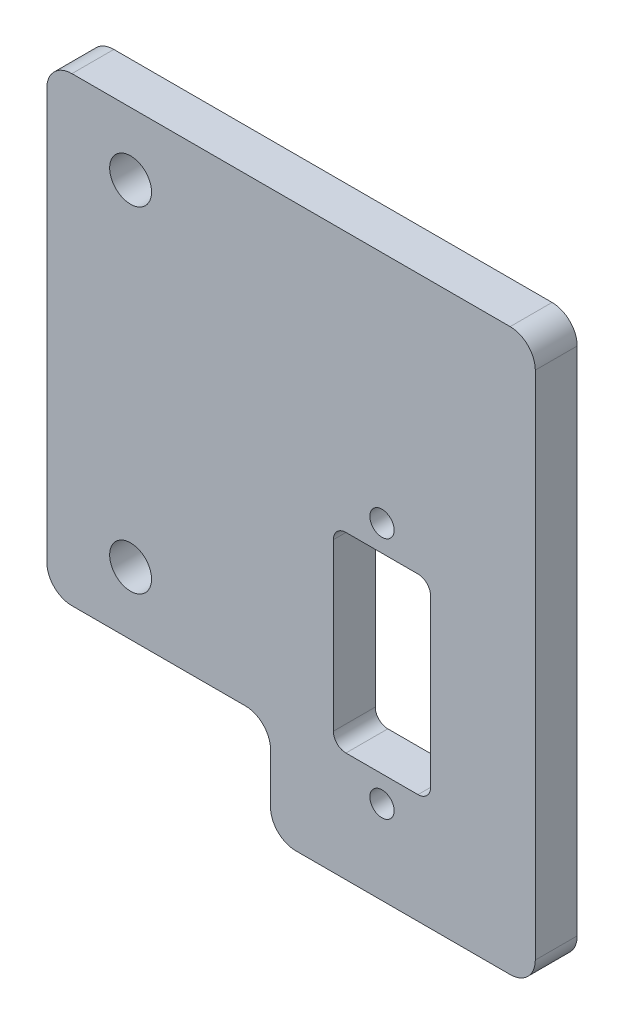
SolidWorks part; units mm, degrees
ref_plane "Front Plane" through (0, 0, 0) normal (0, 0, 1) x (1, 0, 0)
ref_plane "Top Plane" through (0, 0, 0) normal (0, 1, 0) x (1, 0, 0)
ref_plane "Right Plane" through (0, 0, 0) normal (1, 0, 0) x (0, 0, -1)
sketch "Base" plane through (0, 0, 0) normal (0, 0, 1) x (1, 0, 0)
  line L0 (0, 27.5) -> (-26.7, 27.5)
  line L1 (-26.7, 27.5) -> (-26.7, -27.5)
  line L2 (-26.7, -27.5) -> (0, -27.5)
  line L3 (0, -27.5) -> (0, -39.47)
  line L4 (0, -39.47) -> (26.6, -39.47)
  line L5 (26.6, -39.47) -> (26.6, 27.5) construction
  line L8 (-16.7, 20) -> (-16.7, -20) construction
  line L9 (13.3, -0.47) -> (13.3, -29.47) construction
  line L10 (19.1, -3.57) -> (7.5, -3.57)
  line L11 (19.1, -3.57) -> (19.1, -26.37)
  line L12 (19.1, -26.37) -> (7.5, -26.37)
  line L13 (7.5, -3.57) -> (7.5, -26.37)
  line L14 (0, 27.5) -> (26.6, 27.5)
  line L15 (26.6, 27.5) -> (31.6, 27.5)
  line L16 (31.6, 27.5) -> (31.6, -39.47)
  line L17 (31.6, -39.47) -> (26.6, -39.47)
  point P7 (24.1741, 0)
  point P9 (13.3, -39.47)
  point P10 (-26.7, 0)
  point P11 (-16.7, -20)
  point P12 (-16.7, 20)
  point P15 (-16.7, 0)
  point P20 (13.3, -3.57)
  point P21 (13.3, 40)
  point P22 (19.1, -14.97)
  point P23 (13.3, 20)
  point P24 (-16.7, -20)
  point P25 (-16.7, 20)
  point P26 (13.3, -0.47)
  point P27 (13.3, -29.47)
  point P30 (13.3, -14.97)
  point P31 (13.3, -20)
  dimension "D2" = 22.8
  dimension "D1" = 11.6
  dimension "D4" = 30
  dimension "D9" = 29
  dimension "D3" = 40
  dimension "D10" = 6.37
  dimension "D7" = 10
  dimension "D5" = 10
  dimension "D6" = 7.5
  dimension "D8" = 7.5
  dimension "D11" = 5
sketch "Hole_sketch" plane through (0, 0, 0) normal (0, 0, 1) x (1, 0, 0)
  point P0 (-16.7, -20)
  point P2 (-16.7, 20)
  point P4 (13.3, -0.47)
  point P6 (13.3, -29.47)
extrude "Main" add sketch "Base" along normal blind 5
hole_wizard "Gear Axis Holes" positions "Sketch9" profile "Sketch8" hole size "Ø5.0" standard "ANSI Metric" end condition through all
sketch "Sketch9" plane through (0, 0, 0) normal (0, 0, -1) x (-1, 0, 0)
  point P0 (16.7, -20)
  point P3 (16.7, 20)
sketch "Sketch8" plane through (-16.7, -20, 0) normal (1, 0, 0) x (0, 1, 0)
  line L0 (0, 0) -> (0, 5)
  line L1 (0, 5) -> (2.5, 5)
  line L2 (2.5, 5) -> (2.5, 0)
  line L5 (2.5, 0) -> (0, 0)
  line L11 (0, -6.35) -> (0, 107.95) construction
  dimension "Thru Hole Dia." = 5
  dimension "Thru Hole Depth" = 5
hole_wizard "M2.5 Clearance Hole1" positions "Sketch11" profile "Sketch10" hole size "M2.5" standard "ANSI Metric" end condition through all
sketch "Sketch11" plane through (0, 0, 5) normal (0, 0, 1) x (1, 0, 0)
  point P1 (13.3, -0.47)
  point P3 (13.3, -29.47)
sketch "Sketch10" plane through (13.3, -0.47, 5) normal (1, 0, 0) x (0, -1, 0)
  line L0 (0, 0) -> (0, 5)
  line L1 (0, 5) -> (1.45, 5)
  line L2 (1.45, 5) -> (1.45, 0)
  line L5 (1.45, 0) -> (0, 0)
  line L11 (0, -6.35) -> (0, 107.95) construction
  dimension "Thru Hole Dia." = 2.9
  dimension "Thru Hole Depth" = 5
sketch "Sketch13" plane through (0, 0, 5) normal (0, 0, 1) x (1, 0, 0)
  line L1 (7.5, 27.5) -> (7.5, 22.5)
  line L2 (31.6, 27.5) -> (-26.7, 27.5) construction
  line L3 (7.5, 22.5) -> (26.6, 22.5)
  line L4 (26.6, 22.5) -> (26.6, -34.47)
  line L5 (26.6, -34.47) -> (7.5, -34.47)
  line L6 (7.5, -34.47) -> (7.5, -39.47)
  line L7 (7.5, -39.47) -> (31.6, -39.47)
  line L8 (31.6, -39.47) -> (31.6, 27.5)
  line L9 (31.6, 27.5) -> (7.5, 27.5)
  line L10 (0, -39.47) -> (31.6, -39.47) construction
  line L11 (31.6, -39.47) -> (31.6, 27.5) construction
  line L12 (26.6, -39.47) -> (26.6, 27.5) construction
  line L13 (7.5, -3.57) -> (7.5, -26.37) construction
  dimension "D1" = 5
fillet "Fillet1" radius 3 6 edges at (0, -39.47, 2.5) (0, -27.5, 2.5) (-26.7, -27.5, 2.5) (-26.7, 27.5, 2.5) (31.6, 27.5, 2.5) (31.6, -39.47, 2.5)
fillet "Fillet2" radius 1.5 4 edges at (19.1, -26.37, 2.5) (7.5, -26.37, 2.5) (19.1, -3.57, 2.5) (7.5, -3.57, 2.5)
equation "\"D_gear-axes\"= 40mm"
equation "\"D_gear-servo\"= 30mm"
equation "\"W_servo\"= 22.8mm"
equation "\"W_servo-center\"= 6.37mm"
equation "\"D1@Base\" = \"L_servo\""
equation "\"D2@Base\" = \"W_servo\""
equation "\"L_servo\"= 11.6mm"
equation "\"D4@Base\" = \"D_gear-servo\""
equation "\"D9@Base\"=\"W_servo\"+2*(\"D_servo-holes\")"
equation "\"D_servo-holes\"= 3.1mm"
equation "\"D3@Base\"=\"D_gear-axes\""
equation "\"D10@Base\"=\"W_servo-center\""
